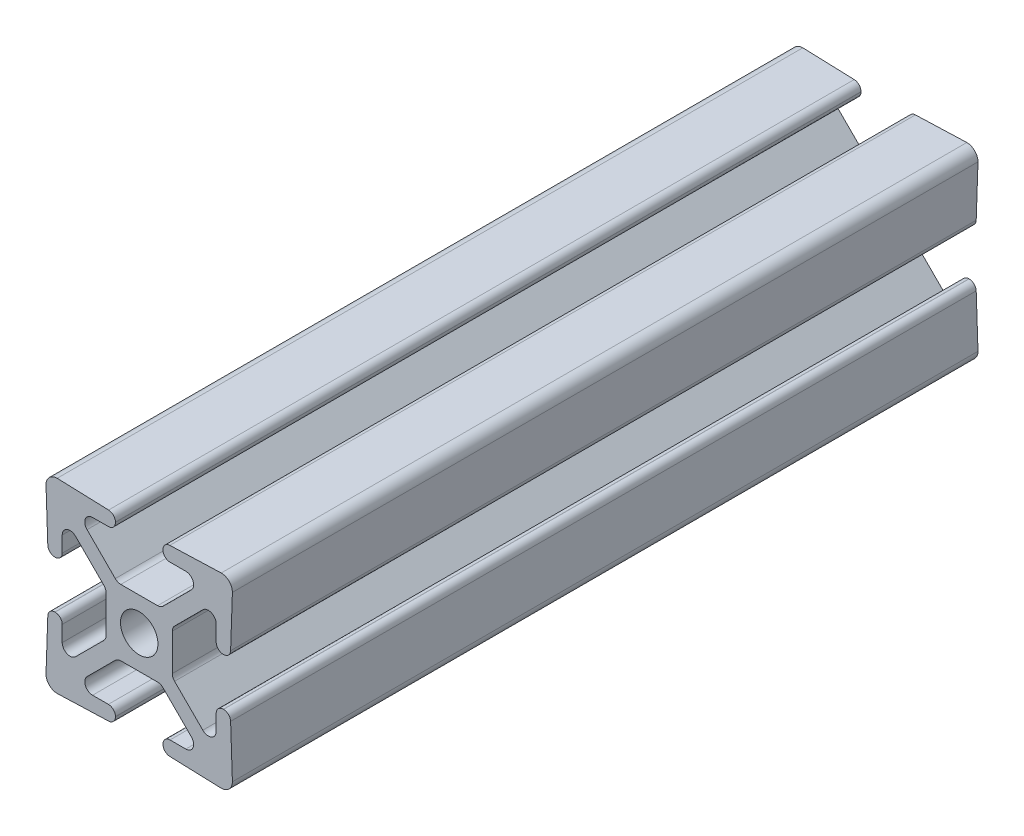
SolidWorks part; units mm, degrees
material "6061 Alloy"
ref_plane "Front Plane" through (0, 0, 0) normal (0, 0, 1) x (1, 0, 0)
ref_plane "Top Plane" through (0, 0, 0) normal (0, 1, 0) x (1, 0, 0)
ref_plane "Right Plane" through (0, 0, 0) normal (1, 0, 0) x (0, 0, -1)
sketch "Sketch1" plane through (0, 0, 0) normal (0, 0, 1) x (1, 0, 0)
  line L1 (3.2385, -11.4554) -> (3.2385, -11.4907)
  line L2 (-7.1065, 8.6691) -> (-3.2584, 4.821)
  line L3 (-3.2385, 11.4907) -> (-3.2385, 11.4554)
  line L6 (-4.2037, 10.4902) -> (-6.3521, 10.4902)
  line L7 (-11.176, 12.7) -> (-4.17, 12.4553)
  line L8 (11.4554, 3.2385) -> (11.4907, 3.2385)
  line L9 (11.4554, -3.2385) -> (11.4907, -3.2385)
  line L11 (-4.821, 3.2584) -> (-8.6691, 7.1065)
  line L12 (-10.4902, 6.3521) -> (-10.4902, 4.2037)
  line L13 (-12.7, 11.176) -> (-12.4553, 4.17)
  line L15 (-4.5085, -2.504) -> (-4.5085, 2.504)
  line L16 (6.3521, -10.4902) -> (4.2037, -10.4902)
  line L22 (-2.504, 4.5085) -> (2.504, 4.5085)
  line L23 (-3.2584, -4.821) -> (-7.1065, -8.6691)
  line L24 (-11.176, -12.7) -> (-4.17, -12.4553)
  line L25 (-12.7, -11.176) -> (-12.4553, -4.17)
  line L26 (-10.4902, -4.2037) -> (-10.4902, -6.3521)
  line L27 (-8.6691, -7.1065) -> (-4.821, -3.2584)
  line L36 (8.6691, -7.1065) -> (4.821, -3.2584)
  line L38 (10.4902, -4.2037) -> (10.4902, -6.3521)
  line L39 (12.7, -11.176) -> (12.4553, -4.17)
  line L42 (11.176, -12.7) -> (4.17, -12.4553)
  line L43 (3.2584, -4.821) -> (7.1065, -8.6691)
  line L47 (4.5085, -2.504) -> (4.5085, 2.504)
  line L48 (12.7, 11.176) -> (12.4553, 4.17)
  line L49 (10.4902, 6.3521) -> (10.4902, 4.2037)
  line L50 (4.821, 3.2584) -> (8.6691, 7.1065)
  line L52 (2.504, -4.5085) -> (-2.504, -4.5085)
  line L56 (11.176, 12.7) -> (4.17, 12.4553)
  line L57 (4.2037, 10.4902) -> (6.3521, 10.4902)
  line L59 (-6.3521, -10.4902) -> (-4.2037, -10.4902)
  line L60 (3.2385, 11.4907) -> (3.2385, 11.4554)
  line L61 (7.1065, 8.6691) -> (3.2584, 4.821)
  line L66 (-11.4554, -3.2385) -> (-11.4907, -3.2385)
  line L68 (-11.4554, 3.2385) -> (-11.4907, 3.2385)
  line L74 (-3.2385, -11.4554) -> (-3.2385, -11.4907)
  arc A1 (-3.2385, 11.4907) -> (-4.17, 12.4553) centre (-4.2037, 11.4907) ccw
  arc A4 (-4.2037, 10.4902) -> (-3.2385, 11.4554) centre (-4.2037, 11.4554) ccw
  arc A6 (-6.3521, 10.4902) -> (-7.1065, 8.6691) centre (-6.3521, 9.4234) ccw
  arc A8 (-12.4553, 4.17) -> (-11.4907, 3.2385) centre (-11.4907, 4.2037) ccw
  arc A9 (-11.176, 12.7) -> (-12.7, 11.176) centre (-11.176, 11.176) ccw
  arc A12 (-8.6691, 7.1065) -> (-10.4902, 6.3521) centre (-9.4234, 6.3521) ccw
  arc A13 (-11.4554, 3.2385) -> (-10.4902, 4.2037) centre (-11.4554, 4.2037) ccw
  arc A16 (-4.821, -3.2584) -> (-4.5085, -2.504) centre (-5.5753, -2.504) ccw
  arc A17 (-4.5085, 2.504) -> (-4.821, 3.2584) centre (-5.5753, 2.504) ccw
  arc A22 (3.2584, 4.821) -> (2.504, 4.5085) centre (2.504, 5.5753) cw
  arc A23 (10.4902, -6.3521) -> (8.6691, -7.1065) centre (9.4234, -6.3521) cw
  arc A24 (10.4902, -4.2037) -> (11.4554, -3.2385) centre (11.4554, -4.2037) cw
  arc A25 (11.4907, -3.2385) -> (12.4553, -4.17) centre (11.4907, -4.2037) cw
  arc A26 (12.7, -11.176) -> (11.176, -12.7) centre (11.176, -11.176) cw
  arc A28 (-2.504, -4.5085) -> (-3.2584, -4.821) centre (-2.504, -5.5753) ccw
  arc A29 (-4.17, -12.4553) -> (-3.2385, -11.4907) centre (-4.2037, -11.4907) ccw
  arc A30 (-3.2385, -11.4554) -> (-4.2037, -10.4902) centre (-4.2037, -11.4554) ccw
  arc A31 (-7.1065, -8.6691) -> (-6.3521, -10.4902) centre (-6.3521, -9.4234) ccw
  arc A32 (-12.7, -11.176) -> (-11.176, -12.7) centre (-11.176, -11.176) ccw
  arc A33 (-11.4907, -3.2385) -> (-12.4553, -4.17) centre (-11.4907, -4.2037) ccw
  arc A34 (-10.4902, -4.2037) -> (-11.4554, -3.2385) centre (-11.4554, -4.2037) ccw
  arc A35 (-10.4902, -6.3521) -> (-8.6691, -7.1065) centre (-9.4234, -6.3521) ccw
  arc A36 (7.1065, -8.6691) -> (6.3521, -10.4902) centre (6.3521, -9.4234) cw
  arc A37 (3.2385, -11.4554) -> (4.2037, -10.4902) centre (4.2037, -11.4554) cw
  arc A38 (-3.2584, 4.821) -> (-2.504, 4.5085) centre (-2.504, 5.5753) ccw
  arc A39 (4.17, -12.4553) -> (3.2385, -11.4907) centre (4.2037, -11.4907) cw
  arc A40 (2.504, -4.5085) -> (3.2584, -4.821) centre (2.504, -5.5753) cw
  circle A44 centre (0, 0) radius 2.5527
  arc A45 (4.5085, 2.504) -> (4.821, 3.2584) centre (5.5753, 2.504) cw
  arc A46 (4.821, -3.2584) -> (4.5085, -2.504) centre (5.5753, -2.504) cw
  arc A47 (11.4554, 3.2385) -> (10.4902, 4.2037) centre (11.4554, 4.2037) cw
  arc A48 (8.6691, 7.1065) -> (10.4902, 6.3521) centre (9.4234, 6.3521) cw
  arc A49 (11.176, 12.7) -> (12.7, 11.176) centre (11.176, 11.176) cw
  arc A53 (12.4553, 4.17) -> (11.4907, 3.2385) centre (11.4907, 4.2037) cw
  arc A54 (6.3521, 10.4902) -> (7.1065, 8.6691) centre (6.3521, 9.4234) cw
  arc A56 (4.2037, 10.4902) -> (3.2385, 11.4554) centre (4.2037, 11.4554) cw
  arc A58 (3.2385, 11.4907) -> (4.17, 12.4553) centre (4.2037, 11.4907) cw
  dimension "D5" = 5.1054
  dimension "D1" = 12.7
  dimension "D2" = 25.4
  dimension "D3" = 25.4
  dimension "D4" = 12.7
extrude "Extrude1" add sketch "Sketch1" along normal blind 101.6
